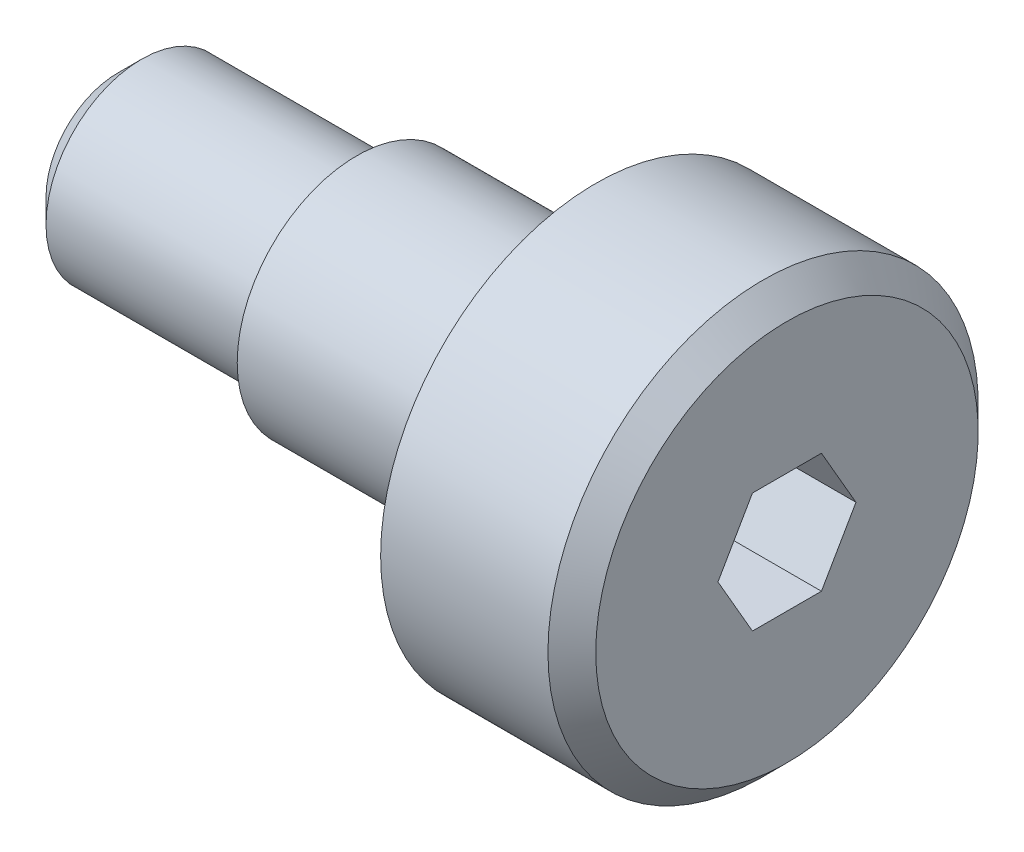
SolidWorks part; units mm, degrees
material "AISI Type 316L stainless steel"
ref_plane "Front Plane" through (0, 0, 0) normal (0, 0, 1) x (1, 0, 0)
ref_plane "Top Plane" through (0, 0, 0) normal (0, 1, 0) x (1, 0, 0)
ref_plane "Right Plane" through (0, 0, 0) normal (1, 0, 0) x (0, 0, -1)
sketch "Sketch1" plane through (0, 0, 0) normal (0, 0, 1) x (1, 0, 0)
  line L0 (0, 0) -> (14, 0)
  line L1 (14, 0) -> (14, 4)
  line L2 (13.5, 4.5) -> (10, 4.5)
  line L3 (10, 4.5) -> (10, 2.5)
  line L4 (10, 2.5) -> (5, 2.5)
  line L5 (5, 2.5) -> (5, 2)
  line L6 (5, 2) -> (0.5, 2)
  line L7 (0, 1.5) -> (0, 0)
  line L8 (0.5, 2) -> (0, 1.5)
  line L9 (14, 4) -> (13.5, 4.5)
  point P4 (14, 4.5)
  point P9 (0, 2)
  dimension "D1" = 5
  dimension "D2" = 2
  dimension "D3" = 5
  dimension "D4" = 2.5
  dimension "D5" = 4
  dimension "D6" = 4.5
revolve "Revolve1" add sketch "Sketch1" angle 360 about L0
sketch "Sketch2" plane through (14, 0, 0) normal (1, 0, 0) x (0, 0, -1)
  line L1 (1.4434, 0) -> (0.7217, 1.25)
  line L2 (0.7217, 1.25) -> (-0.7217, 1.25)
  line L3 (-0.7217, 1.25) -> (-1.4434, 0)
  line L4 (-1.4434, 0) -> (-0.7217, -1.25)
  line L5 (-0.7217, -1.25) -> (0.7217, -1.25)
  line L6 (0.7217, -1.25) -> (1.4434, 0)
  circle A0 centre (0, 0) radius 1.25 construction
  dimension "D1" = 2.5
extrude "Cut-Extrude1" cut sketch "Sketch2" against normal blind 4
move or copy body "Body-Move/Copy1" [suppressed] bodies to move or copy 102 parameters "D1"=0, "D2"=0, "D3"=0
